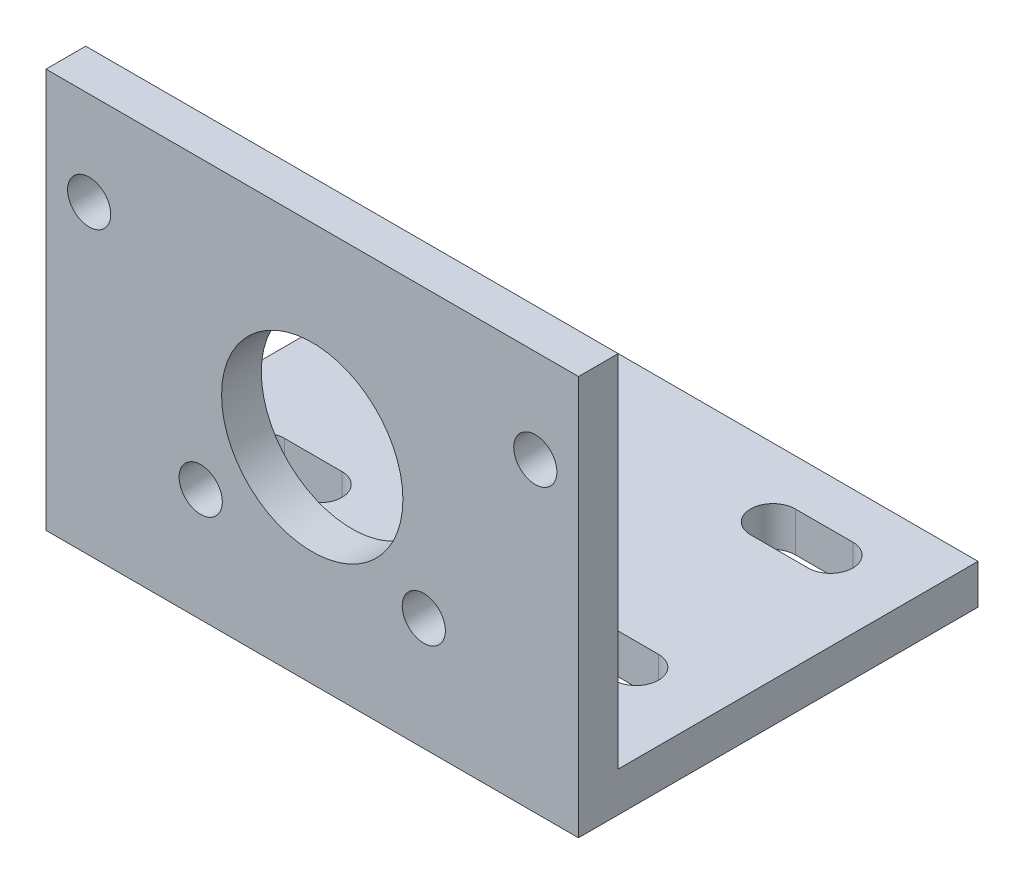
SolidWorks part; units mm, degrees
ref_plane "Front Plane" through (0, 0, 0) normal (0, 0, 1) x (1, 0, 0)
ref_plane "Top Plane" through (0, 0, 0) normal (0, 1, 0) x (1, 0, 0)
ref_plane "Right Plane" through (0, 0, 0) normal (1, 0, 0) x (0, 0, -1)
sketch "Sketch1" plane through (0, 0, 0) normal (1, 0, 0) x (0, 0, -1)
  line L2 (0, 0) -> (0, 27.76)
  line L3 (0, 27.76) -> (2.76, 27.76)
  line L4 (2.76, 2.76) -> (2.76, 27.76)
  line L5 (0, 0) -> (27.76, 0)
  line L7 (2.76, 2.76) -> (27.76, 2.76)
  line L8 (27.76, 0) -> (27.76, 2.76)
  dimension "D3" = 2.76
  dimension "D4" = 25
extrude "Boss-Extrude1" add sketch "Sketch1" along normal mid plane 37
sketch "Sketch2" plane through (0, 0, -2.76) normal (0, 0, -1) x (-1, 0, 0)
  line L0 (-18.5, 2.76) -> (18.5, 2.76) construction
  line L1 (0, 21.26) -> (18.5, 21.26) construction
  circle A0 centre (0, 14.26) radius 6.3
  circle A1 centre (0, 21.26) radius 18.5 construction
  point P2 (15.5, 21.26)
  point P9 (7.75, 7.8366)
  point P12 (-7.75, 7.8366)
  point P13 (-15.5, 21.26)
  point P14 (-7.75, 34.6834)
  point P15 (7.75, 34.6834)
  point P16 (0, 21.26)
  dimension "D2" = 12.6
  dimension "D4" = 37
  dimension "D5" = 15.5
  dimension "D1" = 11.5
  dimension "D3" = 7
  dimension "D6" = 6
extrude "Cut-Extrude1" cut sketch "Sketch2" against normal through all contours A0
hole_wizard "Ø3.0 (3) Diameter Hole1" positions "Sketch3" profile "Sketch4" hole size "Ø3.0" standard "ANSI Metric"
sketch "Sketch3" plane through (0, 0, -2.76) normal (0, 0, -1) x (-1, 0, 0)
  point P0 (15.5, 21.26)
  point P3 (7.75, 7.8366)
  point P6 (-7.75, 7.8366)
  point P9 (-15.5, 21.26)
sketch "Sketch4" plane through (-15.5, 21.26, -2.76) normal (1, 0, 0) x (0, 1, 0)
  line L0 (0, 0) -> (0, 10.9013)
  line L1 (0, 10.9013) -> (1.5, 10)
  line L2 (1.5, 10) -> (1.5, 0)
  line L5 (1.5, 0) -> (0, 0)
  line L10 (0, 10.9013) -> (-1.5, 10) construction
  line L11 (0, -6.35) -> (0, 107.95) construction
  dimension "Hole Dia." = 3
  dimension "Hole Depth" = 10
  dimension "Drill Angle" = 118
sketch "Sketch5" plane through (0, 2.76, 0) normal (0, 1, 0) x (1, 0, 0)
  line L0 (0, 2.76) -> (0, 27.76) construction
  line L1 (18.5, 27.76) -> (-18.5, 27.76) construction
  line L2 (-18.5, 9.51) -> (18.5, 9.51) construction
  line L3 (-18.5, 27.76) -> (-18.5, 2.76) construction
  line L4 (18.5, 27.76) -> (18.5, 2.76) construction
  line L5 (-18.5, 23.01) -> (18.5, 23.01) construction
  line L6 (0, 2.76) -> (-18.5, 2.76) construction
  line L7 (-13, 23.01) -> (-9, 23.01) construction
  line L8 (-13, 24.565) -> (-9, 24.565)
  line L9 (-13, 21.455) -> (-9, 21.455)
  line L10 (-13, 9.51) -> (-9, 9.51) construction
  line L11 (-13, 11.065) -> (-9, 11.065)
  line L12 (-13, 7.955) -> (-9, 7.955)
  line L13 (9, 9.51) -> (13, 9.51) construction
  line L14 (9, 11.065) -> (13, 11.065)
  line L15 (9, 7.955) -> (13, 7.955)
  line L16 (9, 23.01) -> (13, 23.01) construction
  line L17 (9, 24.565) -> (13, 24.565)
  line L18 (9, 21.455) -> (13, 21.455)
  arc A0 (-13, 24.565) -> (-13, 21.455) centre (-13, 23.01) ccw
  arc A1 (-9, 21.455) -> (-9, 24.565) centre (-9, 23.01) ccw
  arc A2 (-13, 11.065) -> (-13, 7.955) centre (-13, 9.51) ccw
  arc A3 (-9, 7.955) -> (-9, 11.065) centre (-9, 9.51) ccw
  arc A4 (9, 11.065) -> (9, 7.955) centre (9, 9.51) ccw
  arc A5 (13, 7.955) -> (13, 11.065) centre (13, 9.51) ccw
  arc A6 (9, 24.565) -> (9, 21.455) centre (9, 23.01) ccw
  arc A7 (13, 21.455) -> (13, 24.565) centre (13, 23.01) ccw
  point P17 (-11, 23.01)
  point P24 (-11, 9.51)
  point P30 (11, 9.51)
  point P37 (11, 23.01)
  point P43 (0, 0)
  point P44 (0, 0)
  point P45 (0, 0)
  point P46 (-11, 23.01)
  dimension "D1" = 13.5
  dimension "D2" = 6.75
  dimension "D3" = 4
  dimension "D4" = 18
  dimension "D5" = 9
  dimension "D6" = 3.11
extrude "Cut-Extrude2" cut sketch "Sketch5" against normal through all
